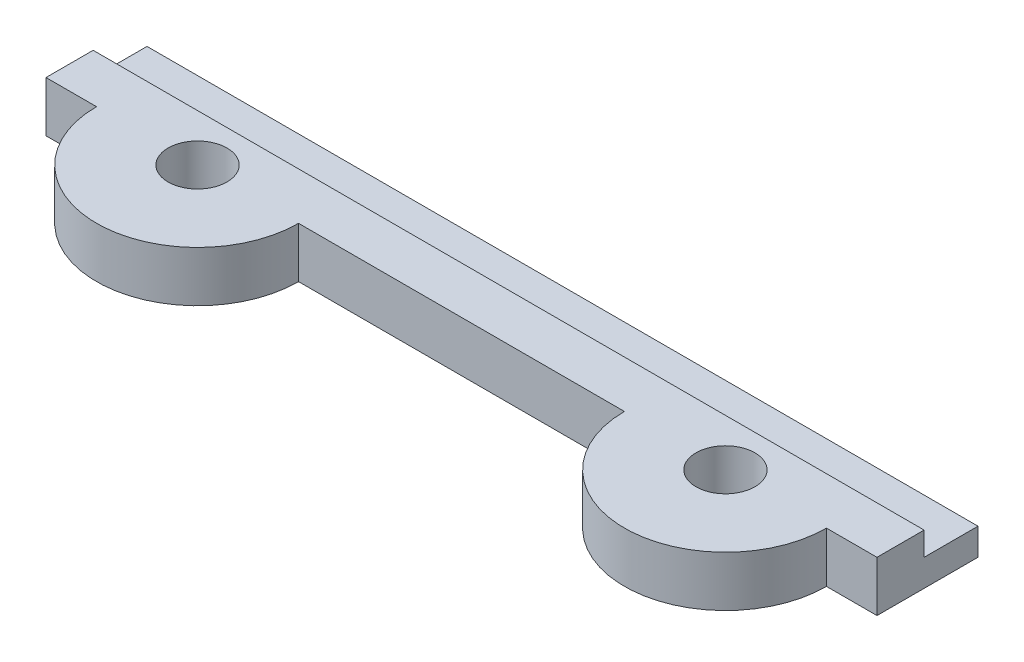
SolidWorks part; units mm, degrees
ref_plane "Спереди" through (0, 0, 0) normal (0, 0, 1) x (1, 0, 0)
ref_plane "Сверху" through (0, 0, 0) normal (0, 1, 0) x (1, 0, 0)
ref_plane "Справа" through (0, 0, 0) normal (1, 0, 0) x (0, 0, -1)
sketch "Эскиз1" plane through (0, 0, 0) normal (0, 1, 0) x (1, 0, 0)
  line L0 (-24.4598, 5.5179) -> (24.896, 5.5179)
  line L1 (9.896, -0.4821) -> (-9.4598, -0.4821)
  line L2 (-21.4598, -0.4821) -> (-24.4598, -0.4821)
  line L3 (-24.4598, -0.4821) -> (-24.4598, 5.5179)
  line L4 (21.896, -0.4821) -> (24.896, -0.4821)
  line L5 (24.896, -0.4821) -> (24.896, 5.5179)
  circle A0 centre (15.896, -0.4821) radius 1.75
  arc A1 (9.896, -0.4821) -> (21.896, -0.4821) centre (15.896, -0.4821) ccw
  circle A2 centre (-15.4598, -0.4821) radius 1.75
  arc A3 (-21.4598, -0.4821) -> (-9.4598, -0.4821) centre (-15.4598, -0.4821) ccw
  dimension "D1" = 6
  dimension "D2" = 6
  dimension "D3" = 3.5
  dimension "D4" = 3.5
  dimension "D5" = 19.3558
  dimension "D6" = 3
  dimension "D7" = 3
extrude "Бобышка-Вытянуть1" add sketch "Эскиз1" along normal blind 3
sketch "Эскиз2" plane through (0, 3, 0) normal (0, 1, 0) x (1, 0, 0)
  line L0 (24.896, -0.4821) -> (24.896, 5.5179) construction
  line L1 (-24.4598, 5.5179) -> (24.896, 5.5179)
  line L2 (-24.4598, 5.5179) -> (-24.4598, 2.3179)
  line L3 (-24.4598, 2.3179) -> (24.896, 2.3179)
  line L4 (24.896, 5.5179) -> (24.896, 2.3179)
  dimension "D1" = 3.2
extrude "Вырез-Вытянуть1" cut sketch "Эскиз2" against normal blind 1.4
